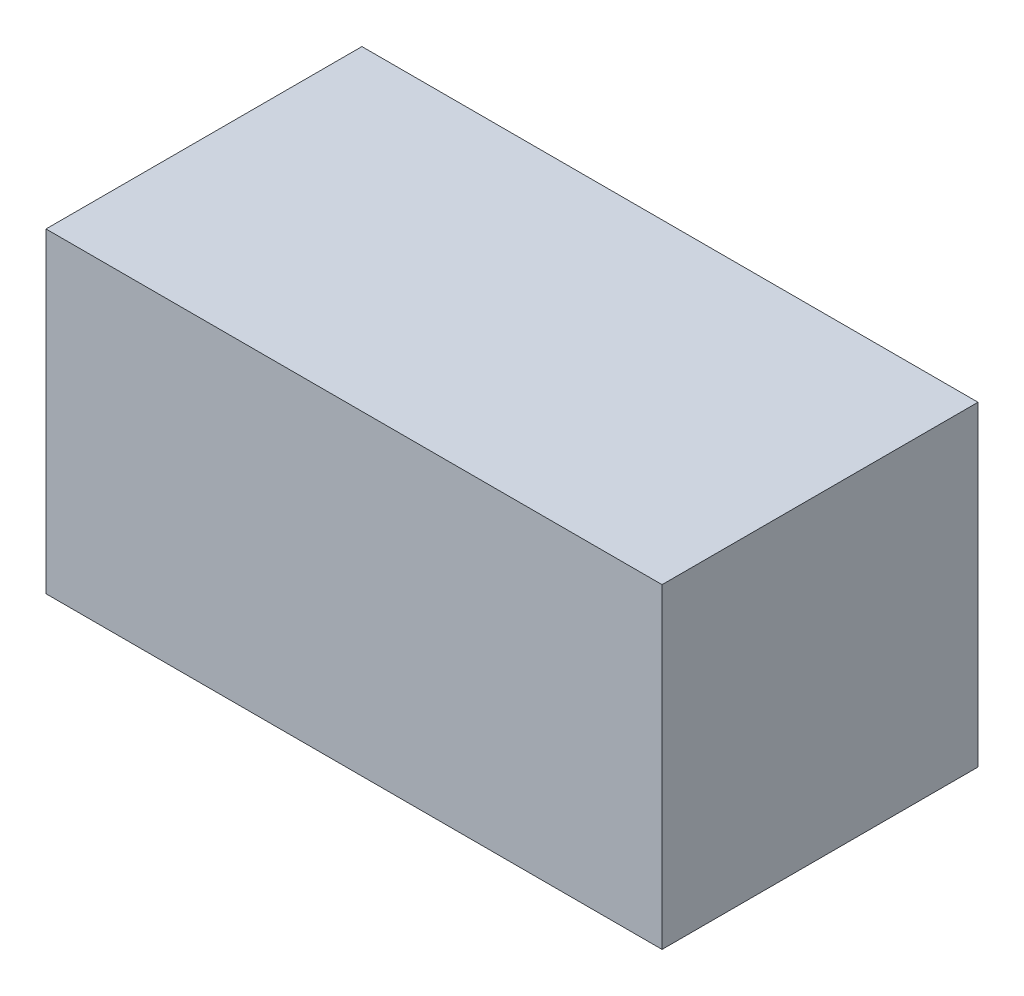
SolidWorks part; units mm, degrees
ref_plane "Front Plane" through (0, 0, 0) normal (0, 0, 1) x (1, 0, 0)
ref_plane "Top Plane" through (0, 0, 0) normal (0, 1, 0) x (1, 0, 0)
ref_plane "Right Plane" through (0, 0, 0) normal (1, 0, 0) x (0, 0, -1)
sketch "Sketch1" plane through (0, 0, 0) normal (0, 1, 0) x (1, 0, 0)
  line L1 (-487.5, 250) -> (487.5, 250)
  line L2 (-487.5, 250) -> (-487.5, -250)
  line L3 (-487.5, -250) -> (487.5, -250)
  line L4 (487.5, 250) -> (487.5, -250)
  line L5 (-487.5, 250) -> (487.5, -250) construction
  line L6 (-487.5, -250) -> (487.5, 250) construction
  point P0 (0, 0)
  dimension "D1" = 500
  dimension "D2" = 975
extrude "Boss-Extrude1" add sketch "Sketch1" along normal blind 500
